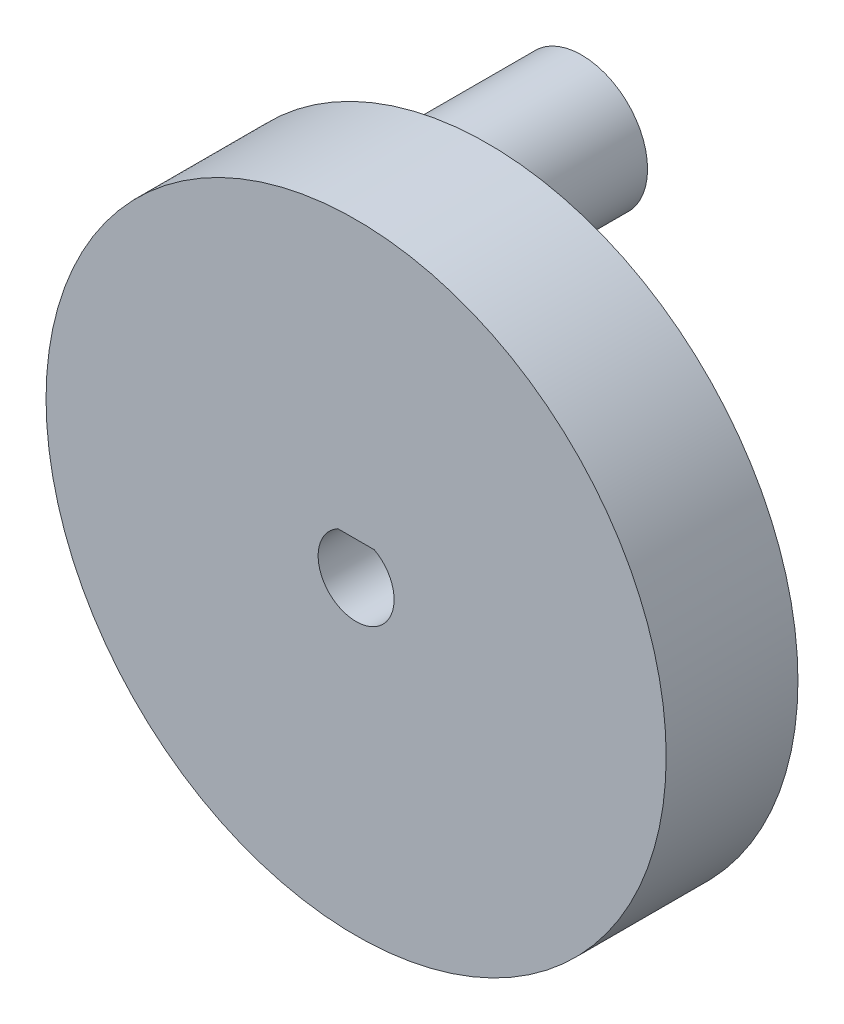
SolidWorks part; units mm, degrees
ref_plane "Alzado" through (0, 0, 0) normal (0, 0, 1) x (1, 0, 0)
ref_plane "Planta" through (0, 0, 0) normal (0, 1, 0) x (1, 0, 0)
ref_plane "Vista lateral" through (0, 0, 0) normal (1, 0, 0) x (0, 0, -1)
sketch "Croquis1" plane through (0, 0, 0) normal (0, 0, 1) x (1, 0, 0)
  line L0 (-1.1747, 2.15) -> (1.1747, 2.15)
  circle A0 centre (0, 0) radius 20
  arc A1 (-1.1747, 2.15) -> (1.1747, 2.15) centre (0, 0) ccw
  point P7 (0, 2.15)
  dimension "D1" = 40
  dimension "D2" = 4.9
extrude "Saliente-Extruir1" add sketch "Croquis1" against normal blind 8.5
sketch "Croquis2" plane through (0, 0, -8.5) normal (0, 0, -1) x (-1, 0, 0)
  circle A0 centre (8.9511, 8.7251) radius 4.25
  circle A2 centre (8.9511, 8.7251) radius 1.5
  dimension "D1" = 8.5
  dimension "D3" = 3
  dimension "D2" = 12.5
extrude "Saliente-Extruir2" add sketch "Croquis2" along normal blind 15
chamfer "Chaflán1" distance 1.5 angle 40 1 edges at (-4.7011, 8.7251, -8.5)
